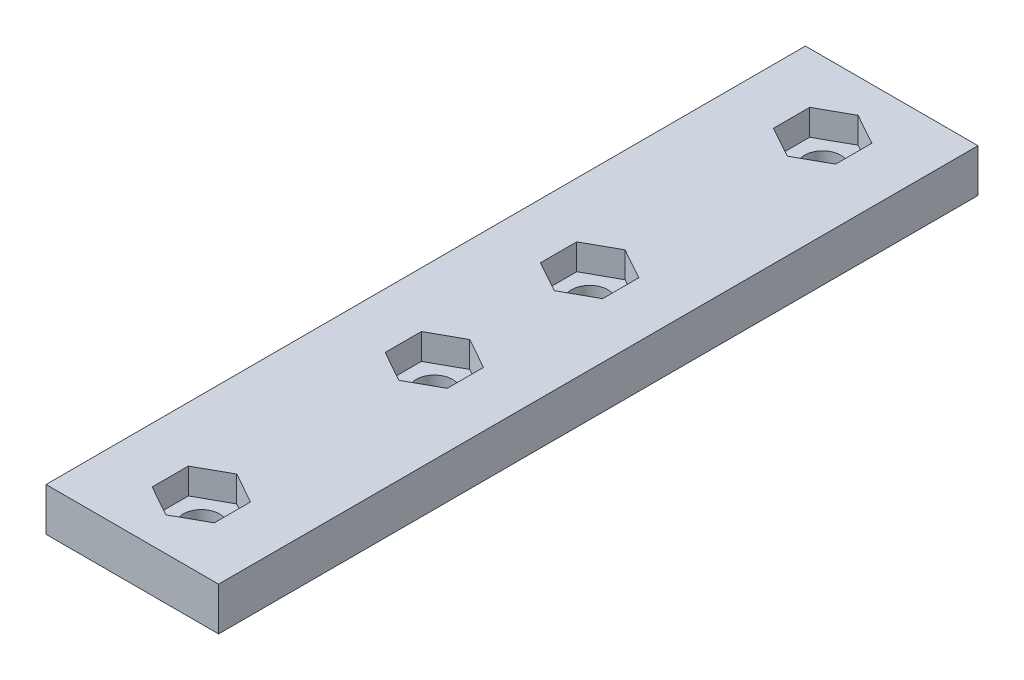
SolidWorks part; units mm, degrees
ref_plane "Front Plane" through (0, 0, 0) normal (0, 0, 1) x (1, 0, 0)
ref_plane "Top Plane" through (0, 0, 0) normal (0, 1, 0) x (1, 0, 0)
ref_plane "Right Plane" through (0, 0, 0) normal (1, 0, 0) x (0, 0, -1)
sketch "Sketch1" plane through (0, 0, 0) normal (0, 1, 0) x (1, 0, 0)
  line L0 (0, 22.5) -> (0, -67.5) construction
  line L1 (-10, -22.5) -> (10, -22.5)
  line L2 (-10, -67.5) -> (-10, 22.5)
  line L3 (-10, 22.5) -> (10, 22.5)
  line L4 (10, -67.5) -> (10, 22.5)
  line L5 (-10, -22.5) -> (10, 22.5) construction
  line L6 (-10, 22.5) -> (10, -22.5) construction
  line L7 (-10, 21.5) -> (10, 21.5)
  line L8 (-10, -66.5) -> (10, -66.5)
  line L9 (-10, -67.5) -> (10, -67.5)
  circle A0 centre (0, 13.5) radius 2.1
  circle A1 centre (0, -13.5) radius 2.1
  circle A2 centre (0, -31.5) radius 2.1
  circle A3 centre (0, -58.5) radius 2.1
  point P0 (0, 0)
  point P19 (0, -22.5)
  point P23 (0, -45)
  dimension "D3" = 4.2
  dimension "D4" = 4.2
  dimension "D5" = 9
  dimension "D6" = 9
  dimension "D1" = 20
  dimension "D2" = 45
  dimension "D7" = 1
extrude "Boss-Extrude1" add sketch "Sketch1" along normal blind 5 contours L7 L2 L1 L4 A1 A0 | L2 L8 L4 L1 A2 A3
sketch "Sketch2" plane through (0, 5, 0) normal (0, 1, 0) x (1, 0, 0)
  line L0 (0, 15.6) -> (0, 17.6) construction
  line L1 (-3.6, 11.4) -> (3.6, 11.4)
  line L2 (-3.6, 11.4) -> (-3.6, 15.6)
  line L3 (-3.6, 15.6) -> (3.6, 15.6)
  line L4 (3.6, 11.4) -> (3.6, 15.6)
  line L5 (-3.6, 11.4) -> (3.6, 15.6) construction
  line L6 (-3.6, 15.6) -> (3.6, 11.4) construction
  line L7 (-3.6, -15.6) -> (3.6, -15.6)
  line L8 (-3.6, -15.6) -> (-3.6, -11.4)
  line L9 (-3.6, -11.4) -> (3.6, -11.4)
  line L10 (3.6, -15.6) -> (3.6, -11.4)
  line L11 (-3.6, -15.6) -> (3.6, -11.4) construction
  line L12 (-3.6, -11.4) -> (3.6, -15.6) construction
  line L13 (-3.6, 13.5) -> (3.6, 13.5) construction
  line L14 (0, -11.4) -> (0, -9.4) construction
  line L15 (-3.6, -13.5) -> (3.6, -13.5) construction
  line L16 (0, 17.6) -> (-3.6, 15.6)
  line L17 (0, 17.6) -> (3.6, 15.6)
  line L18 (0, -9.4) -> (-3.6, -11.4)
  line L19 (0, -9.4) -> (3.6, -11.4)
  line L20 (0, -17.6) -> (-3.6, -15.6)
  line L21 (0, -17.6) -> (3.6, -15.6)
  line L22 (0, 9.4) -> (3.6, 11.4)
  line L23 (0, 9.4) -> (-3.6, 11.4)
  line L24 (-10, -22.5) -> (10, -22.5) construction
  line L25 (-10, -66.5) -> (-10, 21.5) construction
  line L26 (10, -66.5) -> (10, 21.5) construction
  line L27 (-3.6, -29.4) -> (-3.6, -33.6)
  line L28 (0, -27.4) -> (-3.6, -29.4)
  line L29 (0, -27.4) -> (3.6, -29.4)
  line L30 (3.6, -29.4) -> (3.6, -33.6)
  line L31 (0, -35.6) -> (3.6, -33.6)
  line L32 (0, -35.6) -> (-3.6, -33.6)
  line L33 (-3.6, -56.4) -> (-3.6, -60.6)
  line L34 (0, -54.4) -> (-3.6, -56.4)
  line L35 (0, -54.4) -> (3.6, -56.4)
  line L36 (3.6, -56.4) -> (3.6, -60.6)
  line L37 (0, -62.6) -> (3.6, -60.6)
  line L38 (0, -62.6) -> (-3.6, -60.6)
  point P0 (0, 13.5)
  point P6 (0, -13.5)
  circle M22 centre (0, -13.5) radius 2.1
  circle M23 centre (0, 13.5) radius 2.1
  circle M28 centre (0, -31.5) radius 2.1
  circle M29 centre (0, -58.5) radius 2.1
  dimension "D1" = 4.2
  dimension "D2" = 7.2
  dimension "D3" = 4.2
  dimension "D4" = 7.2
  dimension "D5" = 2
  dimension "D6" = 2
extrude "Cut-Extrude1" cut sketch "Sketch2" against normal blind 3 contours L17 L16 L3 | L1 L4 L3 M23 | L3 L2 L1 M23 | L23 L22 L1 | L19 L18 L9 | L7 L10 L9 M22 | L9 L8 L7 M22 | L20 L21 L7 | L32 L31 L30 L29 L28 L27 M28 | L38 L37 L36 L35 L34 L33 M29
